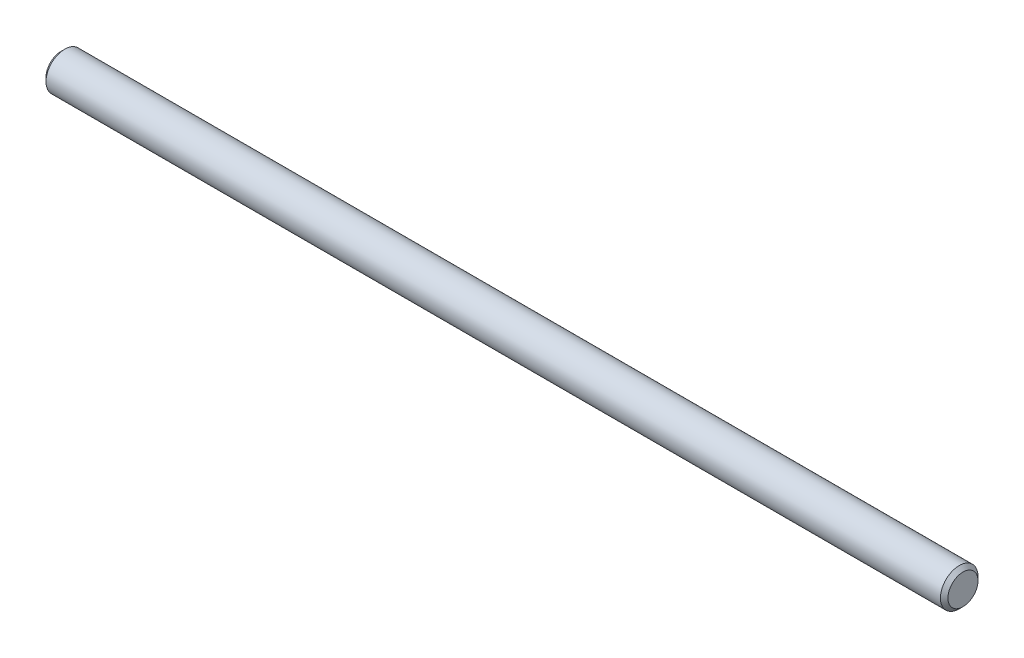
SolidWorks part; units mm, degrees
ref_plane "Front" through (0, 0, 0) normal (0, 0, 1) x (1, 0, 0)
ref_plane "Top" through (0, 0, 0) normal (0, 1, 0) x (1, 0, 0)
ref_plane "Right" through (0, 0, 0) normal (1, 0, 0) x (0, 0, -1)
sketch "Sketch1" plane through (0, 0, 0) normal (0, 0, 1) x (1, 0, 0)
  line L0 (-76.2, 0) -> (76.2, 0) construction
  line L1 (76.2, 3.175) -> (76.2, -3.175) construction
  line L2 (-76.2, 3.175) -> (-76.2, -3.175) construction
  dimension "Length" = 152.4
  dimension "Diameter" = 6.35
sketch "Sketch2" plane through (0, 0, 0) normal (1, 0, 0) x (0, 0, -1)
  circle A0 centre (0, 0) radius 3.175
extrude "Extrude1" add sketch "Sketch2" against normal up to vertex (76.2 mm away) and the other way up to vertex (76.2 mm away) up to point (-76.2, 3.175, 0) other way up to point (76.2, 3.175, 0)
chamfer "Chamfer1" distance 0.635 angle 45 2 edges at (76.2, 0, -3.175) (-76.2, 0, -3.175)
equation "\"D1@Chamfer1\" = \"Diameter@Sketch1\"*.1"
